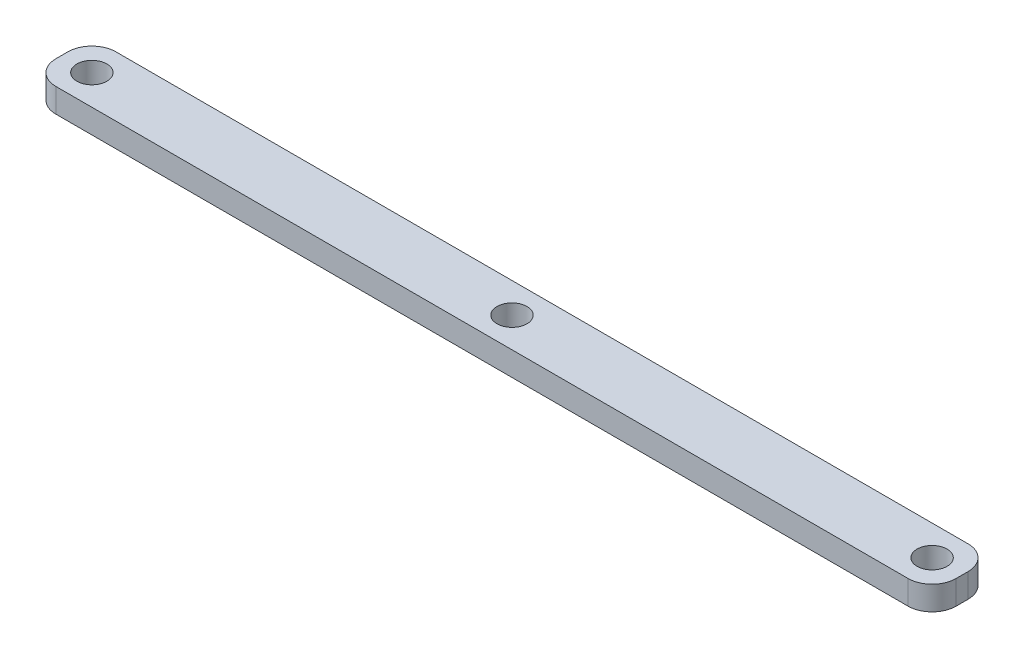
SolidWorks part; units mm, degrees
ref_plane "Alzado" through (0, 0, 0) normal (0, 0, 1) x (1, 0, 0)
ref_plane "Planta" through (0, 0, 0) normal (0, 1, 0) x (1, 0, 0)
ref_plane "Vista lateral" through (0, 0, 0) normal (1, 0, 0) x (0, 0, -1)
sketch "Croquis1" plane through (0, 0, 0) normal (0, 1, 0) x (1, 0, 0)
  line L0 (0, 5) -> (0, -5) construction
  line L1 (-75, -5) -> (75, -5)
  line L2 (-75, -5) -> (-75, 5)
  line L3 (-75, 5) -> (75, 5)
  line L4 (75, -5) -> (75, 5)
  line L5 (-75, -5) -> (75, 5) construction
  line L6 (-75, 5) -> (75, -5) construction
  circle A0 centre (-70, 0) radius 2.5
  circle A1 centre (70, 0) radius 2.5
  circle A2 centre (0, 0) radius 2.5
  point P0 (0, 0)
  dimension "D3" = 5
  dimension "D5" = 5
  dimension "D1" = 150
  dimension "D2" = 10
  dimension "D4" = 5
  dimension "D6" = 5
extrude "Saliente-Extruir1" add sketch "Croquis1" along normal blind 4
fillet "Redondeo1" radius 4 4 edges at (75, 2, 5) (75, 2, -5) (-75, 2, -5) (-75, 2, 5)
